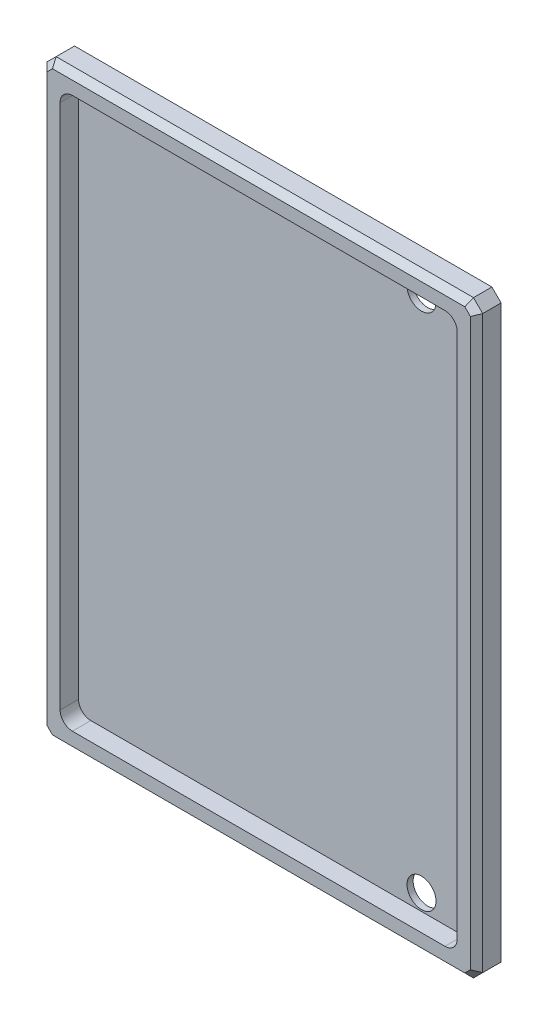
SolidWorks part; units mm, degrees
material "AISI 304"
ref_plane "Front Plane" through (0, 0, 0) normal (0, 0, 1) x (1, 0, 0)
ref_plane "Top Plane" through (0, 0, 0) normal (0, 1, 0) x (1, 0, 0)
ref_plane "Right Plane" through (0, 0, 0) normal (1, 0, 0) x (0, 0, -1)
sketch "Sketch1" plane through (0, 0, 0) normal (0, 0, 1) x (1, 0, 0)
  line L1 (112.7125, -152.4) -> (-112.7125, -152.4)
  line L2 (112.7125, -152.4) -> (112.7125, 152.4)
  line L3 (112.7125, 152.4) -> (-112.7125, 152.4)
  line L4 (-112.7125, -152.4) -> (-112.7125, 152.4)
  line L5 (112.7125, -152.4) -> (-112.7125, 152.4) construction
  line L6 (112.7125, 152.4) -> (-112.7125, -152.4) construction
  point P0 (0, 0)
  dimension "D1" = 304.8
  dimension "D2" = 225.425
extrude "Boss-Extrude1" add sketch "Sketch1" along normal blind 12.7
sketch "Sketch2" plane through (0, 0, 12.7) normal (0, 0, 1) x (1, 0, 0)
  line L0 (-112.7125, 152.4) -> (-112.7125, -152.4) construction
  line L1 (96.3625, -142.4) -> (-96.3625, -142.4)
  line L2 (102.7125, -136.05) -> (102.7125, 136.05)
  line L3 (96.3625, 142.4) -> (-96.3625, 142.4)
  line L4 (-102.7125, -136.05) -> (-102.7125, 136.05)
  line L5 (102.7125, -142.4) -> (-102.7125, 142.4) construction
  line L6 (102.7125, 142.4) -> (-102.7125, -142.4) construction
  line L7 (112.7125, 152.4) -> (-112.7125, 152.4) construction
  arc A0 (-96.3625, -142.4) -> (-102.7125, -136.05) centre (-96.3625, -136.05) cw
  arc A1 (96.3625, -142.4) -> (102.7125, -136.05) centre (96.3625, -136.05) ccw
  arc A2 (102.7125, 136.05) -> (96.3625, 142.4) centre (96.3625, 136.05) ccw
  arc A3 (-96.3625, 142.4) -> (-102.7125, 136.05) centre (-96.3625, 136.05) ccw
  point P0 (0, 0)
  dimension "D3" = 6.35
  dimension "D1" = 10
  dimension "D2" = 10
extrude "Cut-Extrude1" cut sketch "Sketch2" against normal blind 9.525
sketch "Sketch4" plane through (0, 0, 0) normal (0, 0, -1) x (-1, 0, 0)
  line L1 (-112.7125, -152.4) -> (-112.7125, 152.4) construction
  line L2 (0, 0) -> (-117.2439, 0) construction
  line L3 (96.3625, -142.4) -> (-96.3625, -142.4) construction
  circle A0 centre (-74.7125, -134.05) radius 7.5
  circle A1 centre (-74.7125, 134.05) radius 7.5
  dimension "D1" = 15
  dimension "D2" = 8.35
  dimension "D3" = 38
  dimension "D4" = 0
extrude "Cut-Extrude3" cut sketch "Sketch4" against normal through all
hole_wizard "M4x0.7 Tapped Hole1" positions "Sketch10" profile "Sketch11" tap size "M4x0.7" standard "ANSI Metric"
sketch "Sketch10" plane through (0, 0, 0) normal (0, 0, -1) x (-1, 0, 0)
  line L0 (112.7125, 152.4) -> (112.7125, -152.4) construction
  line L1 (-112.7125, 152.4) -> (112.7125, 152.4) construction
  point P0 (107.7125, -113.6)
  point P2 (107.7125, 113.6)
  dimension "D1" = 5
  dimension "D2" = 38.8
  dimension "D3" = 266
cosmetic thread "Hole Thread1" parameters "D1"=6, "D2"=4
cosmetic thread "Hole Thread2" parameters "D1"=6, "D2"=4
sketch "Sketch11" plane through (-107.7125, -113.6, 0) normal (1, 0, 0) x (0, 1, 0)
  line L0 (0, 0) -> (0, 8.9914)
  line L1 (0, 8.9914) -> (1.65, 8)
  line L2 (1.65, 8) -> (1.65, 0)
  line L5 (1.65, 0) -> (0, 0)
  line L10 (0, 8.9914) -> (-1.65, 8) construction
  line L11 (0, -6.35) -> (0, 107.95) construction
  point P3 (0, 0)
  dimension "Tap Drill Dia." = 3.3
  dimension "Tap Drill Depth" = 8
  dimension "Drill Angle" = 118
chamfer "Chamfer1" distance 4.7625 angle 45 8 edges at (0, 152.4, 12.7) (112.7125, 0, 12.7) (-112.7125, 0, 12.7) (0, -152.4, 12.7) (-112.7125, 152.4, 6.35) (112.7125, 152.4, 6.35) (112.7125, -152.4, 6.35) (-112.7125, -152.4, 6.35)
chamfer "Chamfer2" distance 3.175 angle 45 8 edges at (110.3313, -150.0188, 12.7) (112.7125, 0, 12.7) (110.3313, 150.0187, 12.7) (0, 152.4, 12.7) (-110.3312, 150.0187, 12.7) (-112.7125, 0, 12.7) (-110.3313, -150.0188, 12.7) (0, -152.4, 12.7)
